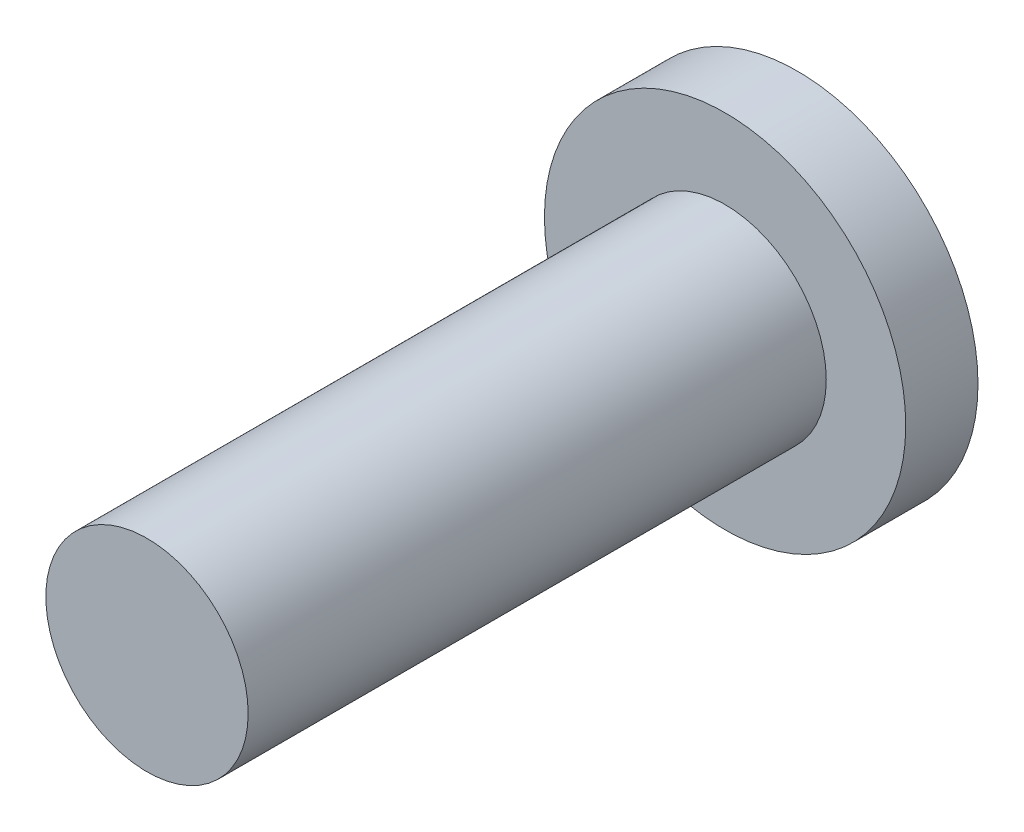
SolidWorks part; units mm, degrees
ref_plane "Front Plane" through (0, 0, 0) normal (0, 0, 1) x (1, 0, 0)
ref_plane "Top Plane" through (0, 0, 0) normal (0, 1, 0) x (1, 0, 0)
ref_plane "Right Plane" through (0, 0, 0) normal (1, 0, 0) x (0, 0, -1)
sketch "Sketch1" plane through (0, 0, 0) normal (0, 0, 1) x (1, 0, 0)
  circle A0 centre (0, 0) radius 1.4
  dimension "D1" = 2.8
extrude "Boss-Extrude1" add sketch "Sketch1" along normal blind 8
sketch "Sketch2" plane through (0, 0, 0) normal (0, 0, 1) x (1, 0, 0)
  circle A0 centre (0, 0) radius 2.5
  dimension "D1" = 5
extrude "Boss-Extrude2" add sketch "Sketch2" against normal blind 1
